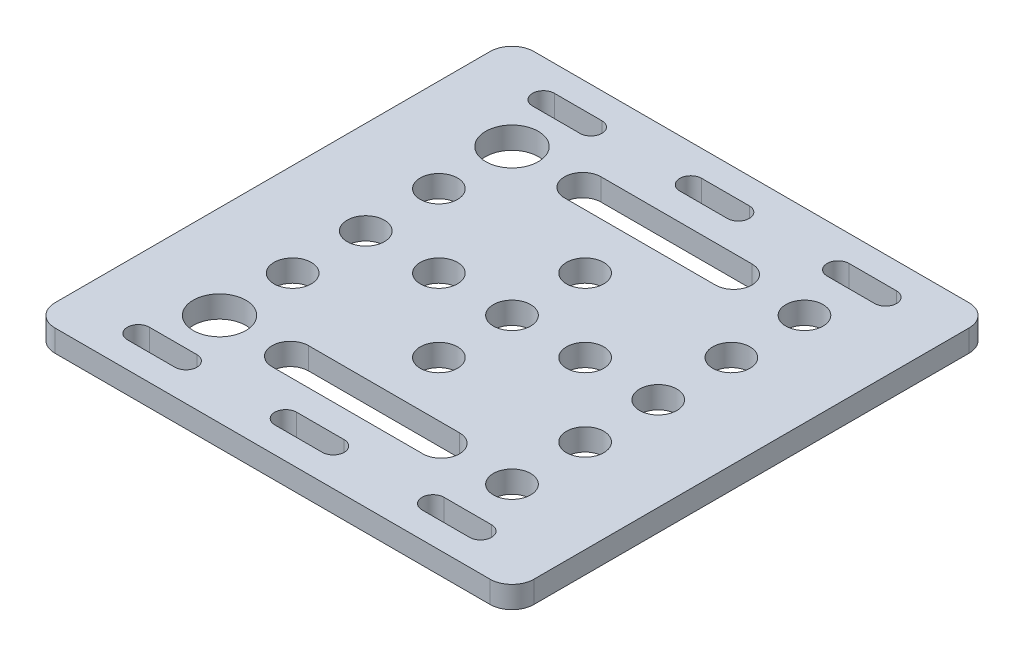
SolidWorks part; units mm, degrees
ref_plane "Front Plane" through (0, 0, 0) normal (0, 0, 1) x (1, 0, 0)
ref_plane "Top Plane" through (0, 0, 0) normal (0, 1, 0) x (1, 0, 0)
ref_plane "Right Plane" through (0, 0, 0) normal (1, 0, 0) x (0, 0, -1)
sketch "Sketch1" plane through (0, 0, 0) normal (0, 1, 0) x (1, 0, 0)
  line L1 (32.75, -32.75) -> (-32.75, -32.75)
  line L2 (32.75, -32.75) -> (32.75, 32.75)
  line L3 (32.75, 32.75) -> (-32.75, 32.75)
  line L4 (-32.75, -32.75) -> (-32.75, 32.75)
  line L5 (32.75, -32.75) -> (-32.75, 32.75) construction
  line L6 (32.75, 32.75) -> (-32.75, -32.75) construction
  point P0 (0, 0)
  dimension "D1" = 65.5
  dimension "D2" = 65.5
extrude "Boss-Extrude1" add sketch "Sketch1" along normal blind 3
sketch "Sketch2" plane through (0, 3, 0) normal (0, 1, 0) x (1, 0, 0)
  line L0 (0, 32.75) -> (0, -32.75) construction
  line L1 (32.75, 32.75) -> (-32.75, 32.75) construction
  line L2 (-32.75, -32.75) -> (32.75, -32.75) construction
  line L3 (32.75, 0) -> (-32.75, 0) construction
  line L4 (32.75, -32.75) -> (32.75, 32.75) construction
  line L5 (-32.75, 32.75) -> (-32.75, -32.75) construction
  line L6 (-20.15, -27.7) -> (-20.15, -26.2) construction
  line L7 (10.32, -17.5) -> (-10.32, -17.5)
  line L8 (0, -17.5) -> (0, -22.5)
  line L9 (10.32, -22.5) -> (-10.32, -22.5)
  line L10 (-10.32, -17.5) -> (-10.32, -22.5)
  line L11 (-16.9, -29.2) -> (-23.4, -29.2)
  line L12 (-16.9, -29.2) -> (-16.9, -26.2)
  line L13 (-16.9, -26.2) -> (-23.4, -26.2)
  line L14 (-23.4, -29.2) -> (-23.4, -26.2)
  line L15 (-16.9, -29.2) -> (-23.4, -26.2) construction
  line L16 (-16.9, -26.2) -> (-23.4, -29.2) construction
  line L17 (-20.15, -26.2) -> (-20.15, -29.2) construction
  line L18 (3.25, -29.2) -> (3.25, -26.2)
  line L19 (3.25, -29.2) -> (-3.25, -29.2)
  line L20 (-3.25, -29.2) -> (-3.25, -26.2)
  line L21 (3.25, -26.2) -> (-3.25, -26.2)
  line L22 (23.4, -29.2) -> (23.4, -26.2)
  line L23 (23.4, -29.2) -> (16.9, -29.2)
  line L24 (16.9, -29.2) -> (16.9, -26.2)
  line L25 (23.4, -26.2) -> (16.9, -26.2)
  line L26 (10.32, -17.5) -> (10.32, -22.5)
  line L27 (10.32, 17.5) -> (10.32, 22.5)
  line L28 (10.32, 17.5) -> (-10.32, 17.5)
  line L29 (-10.32, 17.5) -> (-10.32, 22.5)
  line L30 (10.32, 22.5) -> (-10.32, 22.5)
  line L31 (23.4, 29.2) -> (16.9, 29.2)
  line L32 (16.9, 29.2) -> (16.9, 26.2)
  line L33 (23.4, 26.2) -> (16.9, 26.2)
  line L34 (23.4, 29.2) -> (23.4, 26.2)
  line L35 (3.25, 29.2) -> (-3.25, 29.2)
  line L36 (-3.25, 29.2) -> (-3.25, 26.2)
  line L37 (3.25, 26.2) -> (-3.25, 26.2)
  line L38 (3.25, 29.2) -> (3.25, 26.2)
  line L39 (-16.9, 26.2) -> (-23.4, 26.2)
  line L40 (-23.4, 29.2) -> (-23.4, 26.2)
  line L41 (-16.9, 29.2) -> (-23.4, 29.2)
  line L42 (-16.9, 29.2) -> (-16.9, 26.2)
  circle A0 centre (-20, 0) radius 2.55
  circle A1 centre (-10, 0) radius 2.55
  circle A2 centre (0, 0) radius 2.55
  circle A3 centre (10, 0) radius 2.55
  circle A4 centre (20, 0) radius 2.55
  circle A5 centre (-20, -10) radius 2.55
  circle A6 centre (0, -10) radius 2.55
  circle A7 centre (20, -10) radius 2.55
  circle A8 centre (-20, -20) radius 3.6
  circle A9 centre (-10.32, -20) radius 2.5
  circle A10 centre (-23.4, -27.7) radius 1.5
  circle A11 centre (-16.9, -27.7) radius 1.5
  circle A12 centre (-3.25, -27.7) radius 1.5
  circle A13 centre (3.25, -27.7) radius 1.5
  circle A14 centre (16.9, -27.7) radius 1.5
  circle A15 centre (23.4, -27.7) radius 1.5
  circle A16 centre (10.32, -20) radius 2.5
  circle A17 centre (20, -20) radius 2.55
  circle A18 centre (20, 10) radius 2.55
  circle A19 centre (0, 10) radius 2.55
  circle A20 centre (-20, 10) radius 2.55
  circle A21 centre (-20, 20) radius 3.6
  circle A22 centre (-10.32, 20) radius 2.5
  circle A23 centre (10.32, 20) radius 2.5
  circle A24 centre (20, 20) radius 2.55
  circle A25 centre (23.4, 27.7) radius 1.5
  circle A26 centre (16.9, 27.7) radius 1.5
  circle A27 centre (3.25, 27.7) radius 1.5
  circle A28 centre (-3.25, 27.7) radius 1.5
  circle A29 centre (-16.9, 27.7) radius 1.5
  circle A30 centre (-23.4, 27.7) radius 1.5
  point P36 (-20.15, -27.7)
  dimension "D1" = 5.1
  dimension "D4" = 22.75
  dimension "D5" = 5.1
  dimension "D7" = 12.75
  dimension "D8" = 3
  dimension "D9" = 34.2427
  dimension "D10" = 7.2
  dimension "D11" = 23.7184
  dimension "D12" = 12.75
  dimension "D13" = 10.32
  dimension "D16" = 5
  dimension "D21" = 3
  dimension "D22" = 3
  dimension "D24" = 29.5
  dimension "D25" = 5.1
  dimension "D2" = 12.75
  dimension "D6" = 16.2038
  dimension "D14" = 5
  dimension "D15" = 37.1324
  dimension "D17" = 6.5
  dimension "D18" = 3
  dimension "D19" = 29.0723
  dimension "D20" = 9.35
  dimension "D3" = 5
  dimension "D23" = 3
extrude "Cut-Extrude1" cut sketch "Sketch2" against normal through all contours A30 L40 | A30 L40 | L41 A30 L39 A29 | A29 L42 | A29 L42 | A28 L36 | A28 L36 | L35 A28 L37 A27 | A27 L38 | A27 L38 | A26 L32 | A26 L32 | L31 A26 L33 A25 | A25 L34 | A25 L34 | A21 | A22 L29 | A22 L29 | A23 L30 A22 L28 | L27 A23 | L27 A23 | A24 | A20 | A19 | A18 | A0 | A1 | A2 | A3 | A4 | A5 | A6 | A7 | A8 | L10 A9 | L10 A9 | A9 L9 L8 L7 | L9 A16 L7 L8 | A16 L26 | A16 L26 | A17 | L14 A10 | L14 A10 | A11 L13 A10 L11 | L12 A11 | L12 A11 | L20 A12 | L20 A12 | A13 L21 A12 L19 | L18 A13 | L18 A13 | L24 A14 | L24 A14 | A15 L25 A14 L23 | L22 A15 | L22 A15
fillet "Fillet1" radius 3 4 edges at (32.75, 1.5, 32.75) (32.75, 1.5, -32.75) (-32.75, 1.5, -32.75) (-32.75, 1.5, 32.75)
